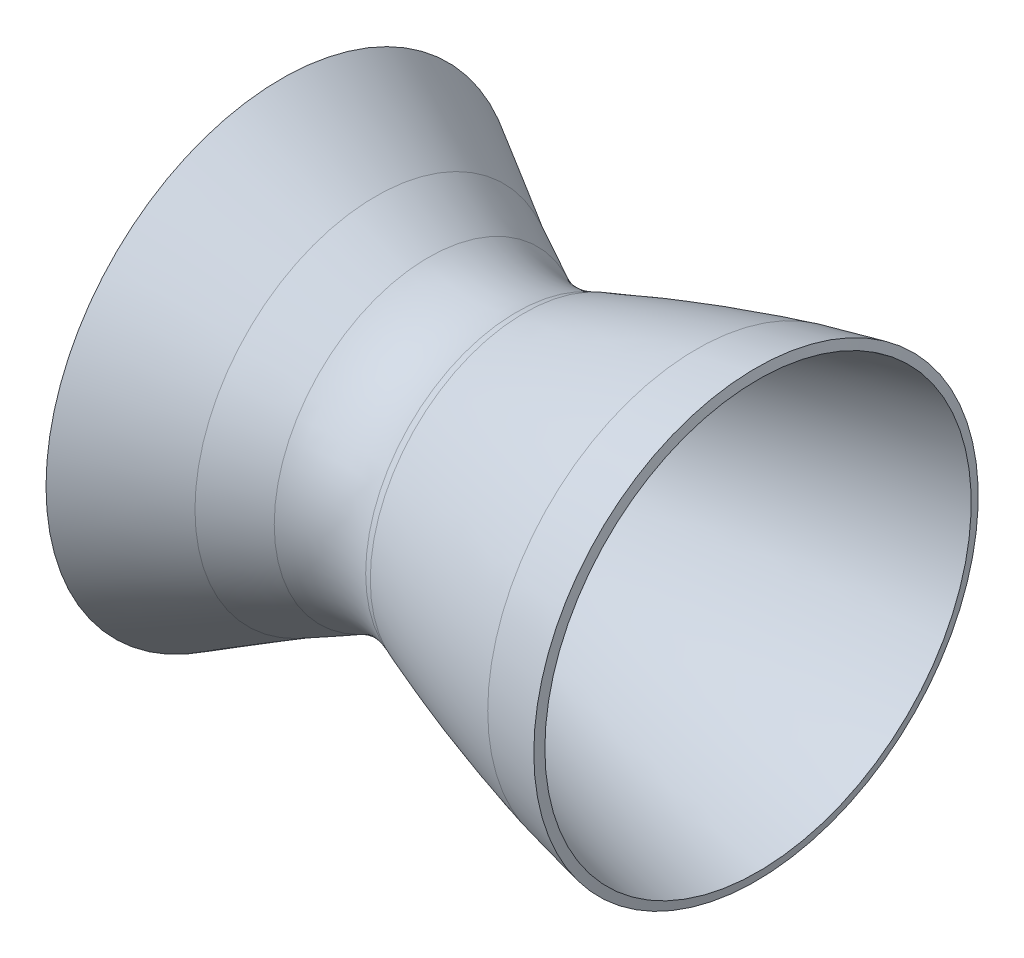
SolidWorks part; units mm, degrees
material "Hexcel AS4C (3000 Filaments)"
ref_plane "Front Plane" through (0, 0, 0) normal (0, 0, 1) x (1, 0, 0)
ref_plane "Top Plane" through (0, 0, 0) normal (0, 1, 0) x (1, 0, 0)
ref_plane "Right Plane" through (0, 0, 0) normal (1, 0, 0) x (0, 0, -1)
sketch "Sketch1" plane through (0, 0, 0) normal (0, 0, 1) x (1, 0, 0)
  line L3 (-89.9348, -48.8612) -> (93.1629, -48.8612) construction
  line L5 (-120.2824, -5.8531) -> (-101.1899, -16.8761)
  line L7 (-120.2824, -5.8531) -> (-142.6516, 6.874)
  line L8 (-24.6836, 3.9045) -> (-25.1855, 6.1418)
  line L9 (-142.6516, 6.874) -> (-142.6516, 9.408)
  line L10 (-142.6516, 9.408) -> (-119.2776, -4.087)
  line L11 (-119.2776, -4.087) -> (-106.252, -10.6799)
  line L12 (-84.4667, -11.5251) -> (-82.5265, -10.7253)
  line L13 (-39.8866, 2.8433) -> (-25.1855, 6.1418)
  arc A0 (-84.4667, -11.5251) -> (-106.252, -10.6799) centre (-94.4373, 12.6624) cw
  arc A2 (-95.5531, -18.6352) -> (-101.1899, -16.8761) centre (-94.4589, -5.2177) cw
  spline S3 degree 3 poles (-95.5531, -18.6352) (-89.8005, -16.2321) (-78.1693, -11.6675) (-54.6915, -3.6257) (-36.7622, 1.2138) (-24.6836, 3.9045) knots 0.017509 0.017509 0.017509 0.017509 0.263132 0.508754 1 1 1 1
  spline S4 degree 3 poles (-82.5265, -10.7253) (-75.5358, -8.0878) (-61.392, -3.1714) (-47.0947, 0.964) (-39.8866, 2.8433) knots 0.214165 0.214165 0.214165 0.214165 0.507949 0.801732 0.801732 0.801732 0.801732
  point P2 (-95.5531, -16.0952)
  dimension "D2" = 26.162
  dimension "D3" = 2.54
  dimension "D1" = 30.226
revolve "Revolve1" add sketch "Sketch1" angle 360 about L3
